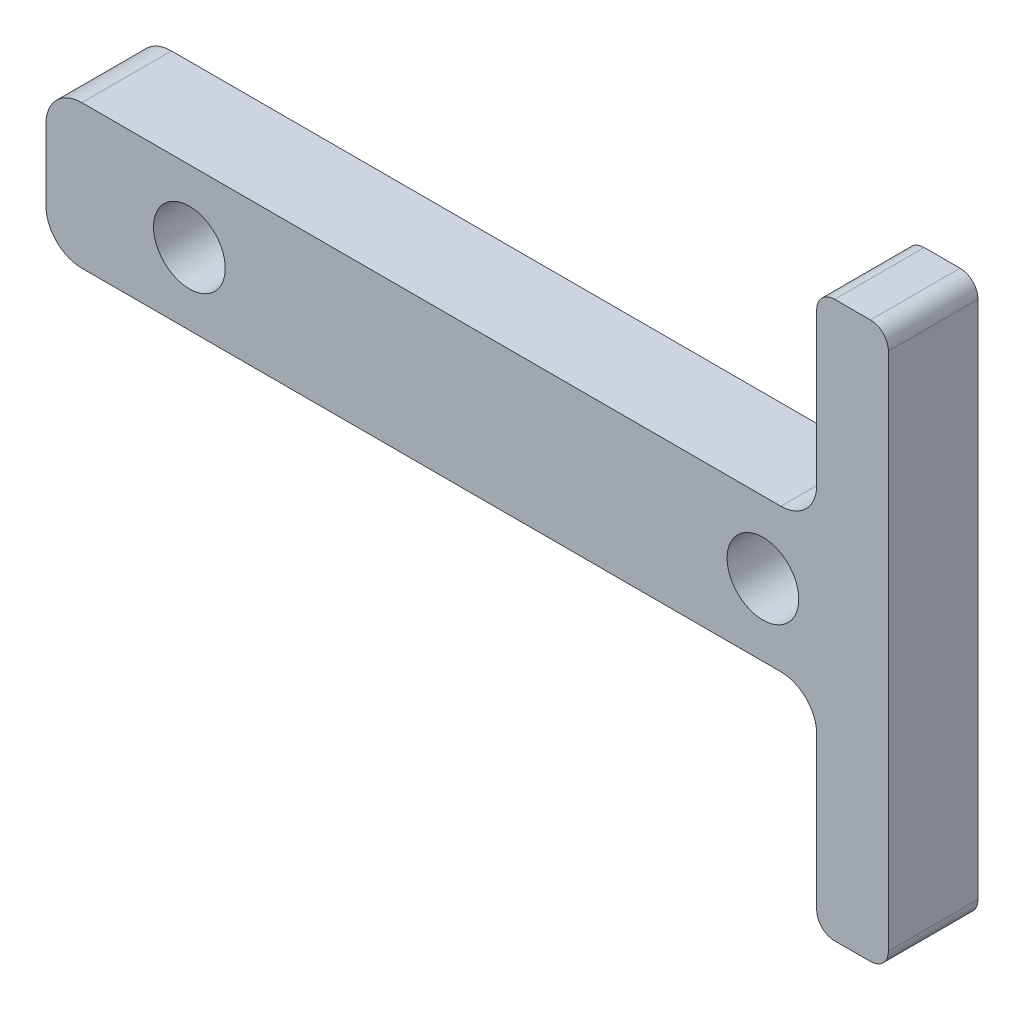
SolidWorks part; units mm, degrees
ref_plane "Front Plane" through (0, 0, 0) normal (0, 0, 1) x (1, 0, 0)
ref_plane "Top Plane" through (0, 0, 0) normal (0, 1, 0) x (1, 0, 0)
ref_plane "Right Plane" through (0, 0, 0) normal (1, 0, 0) x (0, 0, -1)
sketch "Sketch1" plane through (0, 0, 0) normal (0, 0, 1) x (1, 0, 0)
  line L0 (-19.5, 0) -> (19.5, 0)
  line L1 (-19.5, -8) -> (19.5, -8)
  line L2 (-21.5, -2) -> (-21.5, -6)
  line L3 (21.5, 2) -> (21.5, 10.5)
  line L4 (22.5, 11.5) -> (24.5, 11.5)
  line L5 (25.5, 10.5) -> (25.5, -18.5)
  line L6 (-21.5, -4) -> (35.202, -4) construction
  line L7 (21.5, -10) -> (21.5, -18.5)
  line L8 (22.5, -19.5) -> (24.5, -19.5)
  line L9 (-21.5, 0) -> (17.5, 0) construction
  line L10 (-21.5, -8) -> (17.5, -8) construction
  arc A0 (19.5, 0) -> (21.5, 2) centre (19.5, 2) ccw
  arc A1 (19.5, -8) -> (21.5, -10) centre (19.5, -10) cw
  arc A2 (-19.5, -8) -> (-21.5, -6) centre (-19.5, -6) cw
  arc A3 (-19.5, 0) -> (-21.5, -2) centre (-19.5, -2) ccw
  arc A4 (21.5, -18.5) -> (22.5, -19.5) centre (22.5, -18.5) ccw
  arc A5 (24.5, -19.5) -> (25.5, -18.5) centre (24.5, -18.5) ccw
  arc A6 (24.5, 11.5) -> (25.5, 10.5) centre (24.5, 10.5) cw
  arc A7 (21.5, 10.5) -> (22.5, 11.5) centre (22.5, 10.5) cw
  point P4 (0, 0)
  point P14 (25.5, -4)
  point P17 (21.5, 0)
  point P21 (21.5, -8)
  point P30 (21.5, -19.5)
  point P33 (25.5, -19.5)
  point P36 (25.5, 11.5)
  point P39 (21.5, 11.5)
  dimension "D5" = 2
  dimension "D1" = 1
  dimension "D3" = 4
  dimension "D4" = 31
  dimension "D6" = 43
  dimension "D2" = 8
extrude "Boss-Extrude1" add sketch "Sketch1" along normal blind 5
sketch "Sketch2" plane through (0, 0, 5) normal (0, 0, 1) x (1, 0, 0)
  line L0 (23.5, 11.5) -> (23.5, -21.4503) construction
  line L1 (24.5, 11.5) -> (22.5, 11.5) construction
  line L2 (-21.5, -4) -> (29.3804, -4) construction
  line L3 (-21.5, -2) -> (-21.5, -6) construction
  line L4 (21.5, 10.5) -> (21.5, 2) construction
  circle A1 centre (-13.5, -4) radius 2
  circle A2 centre (18.5, -4) radius 2
  dimension "D2" = 4
  dimension "D3" = 4
  dimension "D1" = 35
  dimension "D4" = 32
extrude "Cut-Extrude1" cut sketch "Sketch2" against normal through all
